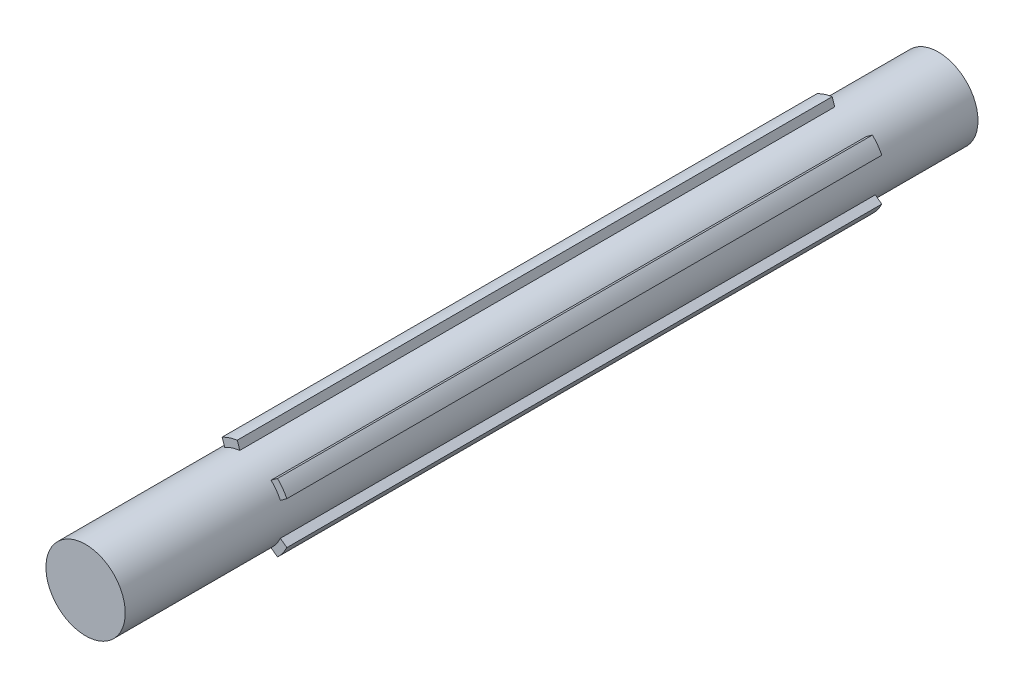
SolidWorks part; units mm, degrees
ref_plane "Ön Düzlem" through (0, 0, 0) normal (0, 0, 1) x (1, 0, 0)
ref_plane "Üst Düzlem" through (0, 0, 0) normal (0, 1, 0) x (1, 0, 0)
ref_plane "Sağ Düzlem" through (0, 0, 0) normal (1, 0, 0) x (0, 0, -1)
sketch "Çizim1" plane through (0, 0, 0) normal (0, 0, 1) x (1, 0, 0)
  circle A0 centre (0, 0) radius 10
  dimension "D1" = 20
extrude "Yükseklik-Ekstrüzyon1" add sketch "Çizim1" against normal blind 215
ref_plane "Düzlem1" through (0, 0, -40) normal (0, 0, 1) x (1, 0, 0)
sketch "Çizim2" plane through (0, 0, -40) normal (0, 0, 1) x (1, 0, 0)
  line L0 (0, 0) -> (-10, 0) construction
  line L1 (-10, 0) -> (-12, 0) construction
  line L2 (-1.7542, 11.8711) -> (-1.1256, 9.9364)
  line L3 (-11.8322, 2) -> (-9.798, 2)
  line L4 (-11.8322, -2) -> (-9.798, -2)
  line L5 (-5.5585, 10.635) -> (-4.9298, 8.7004)
  line L6 (10.748, 5.3367) -> (9.1023, 4.1411)
  line L7 (8.3968, 8.5728) -> (6.7511, 7.3771)
  line L8 (8.3968, -8.5728) -> (6.7511, -7.3771)
  line L9 (10.748, -5.3367) -> (9.1023, -4.1411)
  line L10 (-5.5585, -10.635) -> (-4.9298, -8.7004)
  line L11 (-1.7542, -11.8711) -> (-1.1256, -9.9364)
  circle A0 centre (0, 0) radius 10 construction
  arc A1 (-11.8322, 2) -> (-11.8322, -2) centre (0, 0) ccw
  arc A2 (-1.7542, 11.8711) -> (-5.5585, 10.635) centre (0, 0) ccw
  arc A3 (10.748, 5.3367) -> (8.3968, 8.5728) centre (0, 0) ccw
  arc A4 (8.3968, -8.5728) -> (10.748, -5.3367) centre (0, 0) ccw
  arc A5 (-5.5585, -10.635) -> (-1.7542, -11.8711) centre (0, 0) ccw
  circle A6 centre (0, 0) radius 10
  point P10 (-12, 0)
  point P30 (0, 0)
  dimension "D1" = 24
  dimension "D2" = 2
  dimension "D3" = 2
  dimension "D4" = 5
extrude "Yükseklik-Ekstrüzyon2" add sketch "Çizim2" against normal blind 150 contours A6 L3 A1 L4 | A6 L2 A2 L5 | A6 L6 A3 L7 | A6 L8 A4 L9 | A6 L10 A5 L11
